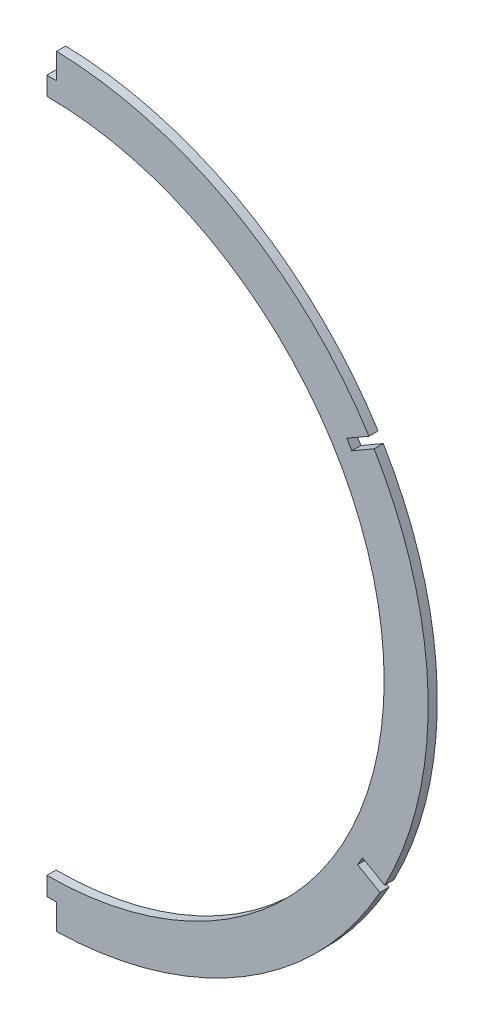
SolidWorks part; units mm, degrees
material "Plywood"
ref_plane "Front Plane" through (0, 0, 0) normal (0, 0, 1) x (1, 0, 0)
ref_plane "Top Plane" through (0, 0, 0) normal (0, 1, 0) x (1, 0, 0)
ref_plane "Right Plane" through (0, 0, 0) normal (1, 0, 0) x (0, 0, -1)
sketch "Sketch2" plane through (0, 0, 0) normal (0, 0, 1) x (1, 0, 0)
  line L0 (0, 0) -> (0, 236.6718) construction
  line L1 (-1.651, 128.5137) -> (-1.651, 121.4017) construction
  line L3 (1.651, 128.5137) -> (1.651, 121.4017) construction
  line L4 (-1.651, 121.4017) -> (1.651, 121.4017) construction
  line L5 (-136.2041, -77.9016) -> (0, 0.7359) construction
  line L6 (-136.2041, -77.9016) -> (0, 0.7359) construction
  line L7 (136.2041, -77.9016) -> (0, 0.7359) construction
  line L8 (136.2041, -77.9016) -> (0, 0.7359) construction
  line L9 (-116.9741, -64.8927) -> (-110.0155, -60.8752) construction
  line L10 (-115.4036, -67.7988) -> (-108.3645, -63.7348) construction
  line L11 (-110.0155, -60.8752) -> (-108.3645, -63.7348) construction
  line L12 (-117.55, -65.2252) -> (-116.9741, -64.8927) construction
  line L13 (-115.899, -68.0849) -> (-115.4036, -67.7988) construction
  line L14 (115.4036, -67.7988) -> (109.2442, -64.2427) construction
  line L15 (110.8952, -61.3831) -> (109.2442, -64.2427) construction
  line L16 (116.9741, -64.8927) -> (110.8952, -61.3831) construction
  arc A0 (-1.651, 128.5137) -> (-116.9741, -64.8927) centre (0, -3.556) ccw
  arc A1 (0.0665, 128.1531) -> (63.0696, -118.8475) centre (0, -3.3993) ccw construction
  circle A2 centre (0, -3.556) radius 116.84
  arc A3 (63.0696, -118.8475) -> (0.0665, 128.1531) centre (0, -3.3993) ccw construction
  arc A4 (0, 128.524) -> (-1.651, 128.5137) centre (0, -3.556) ccw
  circle A5 centre (0, -3.556) radius 132.08 construction
  arc A6 (1.651, 128.5137) -> (0, 128.524) centre (0, -3.556) ccw
  arc A7 (-116.9741, -64.8927) -> (-116.1978, -66.3509) centre (0, -3.556) ccw
  arc A8 (-115.4036, -67.7988) -> (115.4036, -67.7988) centre (0, -3.556) ccw
  arc A9 (-116.1978, -66.3509) -> (-115.4036, -67.7988) centre (0, -3.556) ccw
  arc A10 (115.4036, -67.7988) -> (116.1978, -66.3509) centre (0, -3.556) ccw
  arc A11 (116.9741, -64.8927) -> (1.651, 128.5137) centre (0, -3.556) ccw
  arc A12 (116.1978, -66.3509) -> (116.9741, -64.8927) centre (0, -3.556) ccw
  point P24 (-115.4036, -67.7988)
  dimension "D1" = 3.556
  dimension "D3" = 264.16
  dimension "D2" = 15.24
  dimension "D4" = 3.302
  dimension "D5" = 7.112
  dimension "D6" = 3.302
  dimension "D7" = 8.128
  dimension "D8" = 7.076
extrude "Boss-Extrude1" add sketch "Sketch2" along normal mid plane 3.175
sketch "Sketch3" plane through (0, 0, 0) normal (1, 0, 0) x (0, 0, -1)
  line L1 (-109.3908, 192.564) -> (122.8198, 192.564)
  line L2 (-109.3908, 192.564) -> (-109.3908, -206.3906)
  line L3 (-109.3908, -206.3906) -> (122.8198, -206.3906)
  line L4 (122.8198, 192.564) -> (122.8198, -206.3906)
extrude "Cut-Extrude1" cut sketch "Sketch3" against normal through all
sketch "Sketch4" plane through (0, 0, 1.5875) normal (0, 0, 1) x (1, 0, 0)
  line L0 (0, 0) -> (0, 113.284) construction
  line L1 (0, 113.284) -> (0, 119.634) construction
  line L2 (-99.2768, 58.0533) -> (-104.776, 61.2283) construction
  line L3 (3.3782, 119.634) -> (-3.3782, 119.634)
  line L4 (0, 119.634) -> (0, 129.794)
  line L5 (3.3782, 129.794) -> (-3.3782, 129.794)
  line L6 (-3.3782, 119.634) -> (-3.3782, 129.794)
  line L7 (-105.6206, 59.7655) -> (-103.9315, 62.6911)
  line L8 (7.6459, 0.7359) -> (-7.6459, 0.7359) construction
  line L9 (-103.9315, 62.6911) -> (-112.7303, 67.7711)
  line L10 (102.9936, -58.7275) -> (108.4929, -61.9025) construction
  line L11 (-130.6719, 76.1793) -> (0, 0.7359) construction
  line L12 (-112.7303, 67.7711) -> (-114.4194, 64.8455)
  line L13 (-130.6719, -74.7076) -> (0, 0.7359) construction
  line L14 (0, 0.7359) -> (0, -120.396) construction
  line L15 (0, -120.396) -> (0, -126.746) construction
  line L16 (0, 128.524) -> (0, 113.284) construction
  line L17 (-102.9936, -58.7275) -> (-108.4929, -61.9025) construction
  line L18 (3.3782, -126.746) -> (-3.3782, -126.746)
  line L19 (0, -126.746) -> (0, -136.906)
  line L20 (3.3782, -136.906) -> (-3.3782, -136.906)
  line L21 (-3.3782, -126.746) -> (-3.3782, -136.906)
  line L22 (-107.6483, -63.3653) -> (-109.3374, -60.4397)
  line L23 (-109.3374, -60.4397) -> (-118.1363, -65.5197)
  line L24 (-118.1363, -65.5197) -> (-116.4472, -68.4453)
  line L25 (-107.6483, -63.3653) -> (-116.4472, -68.4453)
  line L26 (-105.6206, 59.7655) -> (-114.4194, 64.8455)
  line L27 (130.6719, -74.7076) -> (0, 0.7359) construction
  line L28 (130.6719, 76.1793) -> (0, 0.7359) construction
  line L29 (99.2768, 58.0533) -> (104.776, 61.2283) construction
  line L30 (105.6206, 59.7655) -> (114.4194, 64.8455)
  line L31 (107.6483, -63.3653) -> (116.4472, -68.4453)
  line L32 (118.1363, -65.5197) -> (116.4472, -68.4453)
  line L33 (109.3374, -60.4397) -> (118.1363, -65.5197)
  line L34 (107.6483, -63.3653) -> (109.3374, -60.4397)
  line L35 (3.3782, -126.746) -> (3.3782, -136.906)
  line L36 (112.7303, 67.7711) -> (114.4194, 64.8455)
  line L37 (103.9315, 62.6911) -> (112.7303, 67.7711)
  line L38 (105.6206, 59.7655) -> (103.9315, 62.6911)
  line L39 (3.3782, 119.634) -> (3.3782, 129.794)
  point P18 (-102.9936, -58.7275)
  point P23 (-99.2768, 58.0533)
  point P30 (-117.2917, -66.9825)
  point P32 (-113.5748, 66.3083)
  point P53 (113.5748, 66.3083)
  point P54 (117.2917, -66.9825)
  point P55 (99.2768, 58.0533)
  point P56 (102.9936, -58.7275)
  arc M6 (0, -135.636) -> (0, 128.524) centre (0, -3.556) ccw
  line M7 (0, 128.524) -> (0, 113.284)
  line M9 (0, -120.396) -> (0, -135.636)
  dimension "D1" = 113.284
  dimension "D2" = 6.35
  dimension "D3" = 10.16
  dimension "D4" = 3.3782
  dimension "D5" = 0.7359
  dimension "D6" = 60
  dimension "D7" = 121.1319
  dimension "D8" = 6.35
  dimension "D9" = 10.16
  dimension "D10" = 3.3782
  dimension "D11" = 118.9268
  dimension "D12" = 6.35
  dimension "D13" = 10.16
  dimension "D14" = 1.6891
  dimension "D15" = 114.6349
  dimension "D16" = 6.35
  dimension "D17" = 1.6891
  dimension "D18" = 10.16
extrude "Cut-Extrude2" cut sketch "Sketch4" against normal through all contours L3 L39 M6 M7 | L38 L30 L37 M6 | L34 L31 L33 M6 | L35 L18 M9 M6
